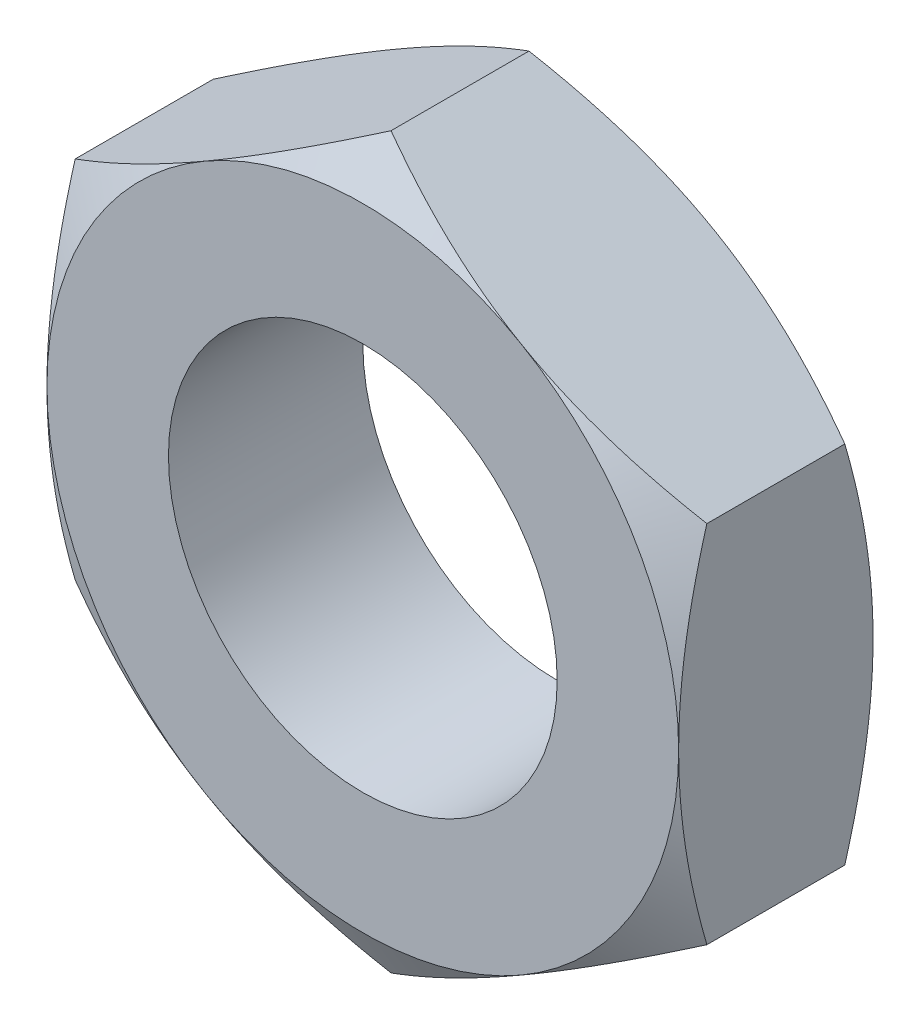
SolidWorks part; units mm, degrees
material "1.4000 (X6Cr13)"
ref_plane "Płaszczyzna XY" through (0, 0, 0) normal (0, 0, 1) x (1, 0, 0)
ref_plane "Płaszczyzna XZ" through (0, 0, 0) normal (0, 1, 0) x (1, 0, 0)
ref_plane "Płaszczyzna YZ" through (0, 0, 0) normal (1, 0, 0) x (0, 0, -1)
sketch "Szkic1" plane through (0, 0, 0) normal (0, 0, 1) x (1, 0, 0)
  line L1 (6.5, 3.7528) -> (0, 7.5056)
  line L2 (0, 7.5056) -> (-6.5, 3.7528)
  line L3 (-6.5, 3.7528) -> (-6.5, -3.7528)
  line L4 (-6.5, -3.7528) -> (0, -7.5056)
  line L5 (0, -7.5056) -> (6.5, -3.7528)
  line L6 (6.5, -3.7528) -> (6.5, 3.7528)
  circle A0 centre (0, 0) radius 6.5 construction
  circle A1 centre (0, 0) radius 4
  dimension "D2" = 8
  dimension "D1" = 13
extrude "Dodanie-wyciągnięcie1" add sketch "Szkic1" along normal blind 4
sketch "Szkic2" plane through (0, 0, 0) normal (0, 1, 0) x (1, 0, 0)
  line L0 (-6.5, -4) -> (-6.5, 0)
  line L1 (-6.5, -4) -> (-6.5, 0) construction
  line L2 (4, 0) -> (4, -4)
  line L3 (-3, -4) -> (-3, 0)
  line L5 (4, 0) -> (4, -4)
  line L6 (-6.5, -4) -> (-9.9641, -2)
  line L7 (-6.5, -4) -> (-3, -4)
  line L8 (-9.9641, -2) -> (-6.5, 0)
  line L9 (0, -9.8911) -> (0, 0.9366) construction
  line L11 (-6.5, -4) -> (-9.9641, -4)
  line L13 (-6.5, 0) -> (-9.9641, 0)
  line L14 (-9.9641, -4) -> (-9.9641, 0)
  dimension "D1" = 30
  dimension "D2" = 60
revolve "Wycięcie-obrót1" cut sketch "Szkic2" angle 360 about L9
